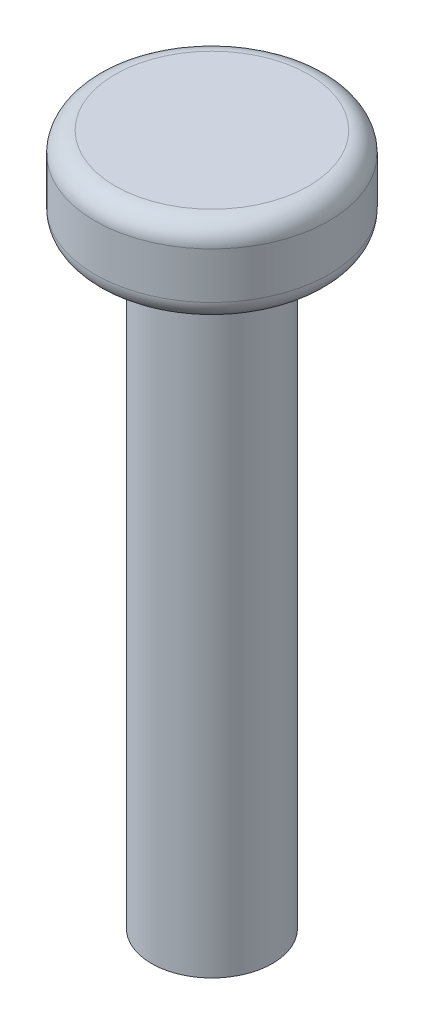
SolidWorks part; units mm, degrees
ref_plane "Спереди" through (0, 0, 0) normal (0, 0, 1) x (1, 0, 0)
ref_plane "Сверху" through (0, 0, 0) normal (0, 1, 0) x (1, 0, 0)
ref_plane "Справа" through (0, 0, 0) normal (1, 0, 0) x (0, 0, -1)
sketch "Sketch1" plane through (0, 0, 0) normal (0, 1, 0) x (1, 0, 0)
  circle A0 centre (0, 0) radius 3
  dimension "D1" = 6
extrude "Boss-Extrude1" add sketch "Sketch1" along normal blind 30
sketch "Sketch2" plane through (0, 30, 0) normal (0, 1, 0) x (1, 0, 0)
  circle A0 centre (0, 0) radius 5.8
  dimension "D1" = 11.6
extrude "Boss-Extrude2" add sketch "Sketch2" along normal blind 4.3
fillet "Fillet1" radius 1 2 edges at (0, 30, 5.8) (0, 34.3, 5.8)
